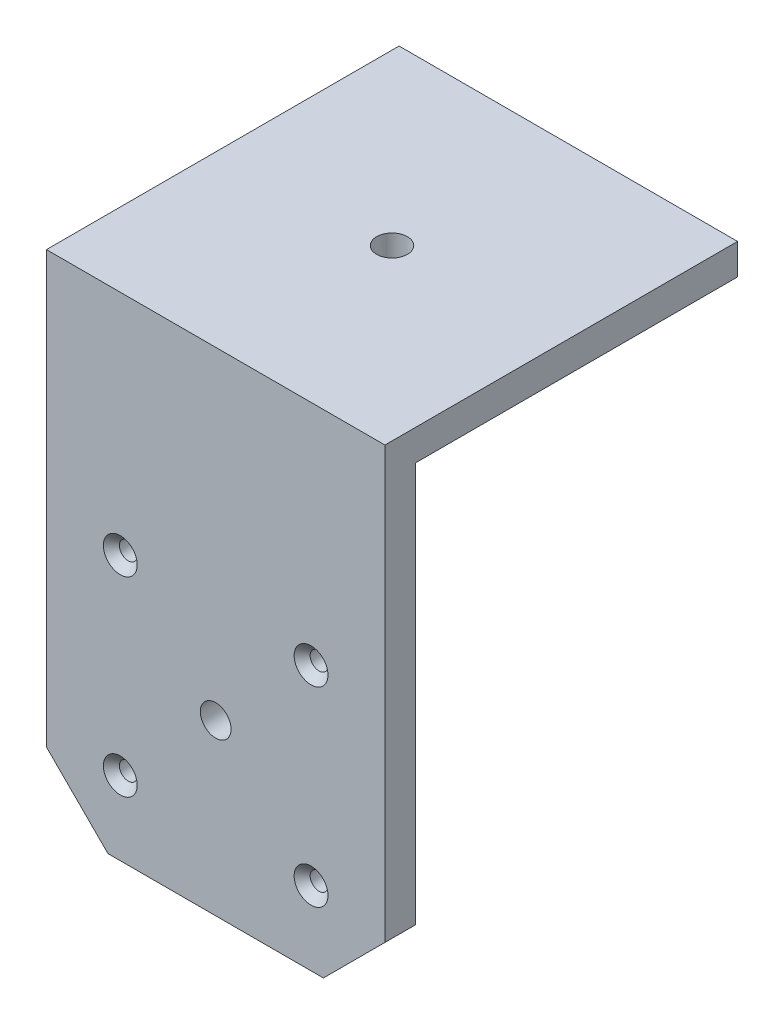
SolidWorks part; units mm, degrees
ref_plane "Ön Düzlem" through (0, 0, 0) normal (0, 0, 1) x (1, 0, 0)
ref_plane "Üst Düzlem" through (0, 0, 0) normal (0, 1, 0) x (1, 0, 0)
ref_plane "Sağ Düzlem" through (0, 0, 0) normal (1, 0, 0) x (0, 0, -1)
sketch "Sketch1" plane through (0, 0, 0) normal (0, 1, 0) x (1, 0, 0)
  line L1 (-27.5, 28.65) -> (27.5, 28.65)
  line L2 (-27.5, 28.65) -> (-27.5, -28.65)
  line L3 (-27.5, -28.65) -> (27.5, -28.65)
  line L4 (27.5, 28.65) -> (27.5, -28.65)
  line L5 (-27.5, 28.65) -> (27.5, -28.65) construction
  line L6 (-27.5, -28.65) -> (27.5, 28.65) construction
  circle A0 centre (0, 0) radius 2.5
  point P0 (0, 0)
  dimension "D1" = 55
  dimension "D2" = 57.3
extrude "Boss-Extrude1" add sketch "Sketch1" along normal blind 5
sketch "Sketch2" plane through (0, 0, 0) normal (0, -1, 0) x (1, 0, 0)
  line L0 (27.5, 28.65) -> (27.5, -28.65) construction
  line L1 (-27.5, 28.65) -> (27.5, 28.65)
  line L2 (-27.5, 28.65) -> (-27.5, 23.65)
  line L3 (-27.5, 23.65) -> (27.5, 23.65)
  line L4 (27.5, 28.65) -> (27.5, 23.65)
  line L6 (-27.5, -28.65) -> (27.5, -28.65)
  line L7 (-27.5, -28.65) -> (-27.5, -23.65)
  line L8 (-27.5, -23.65) -> (27.5, -23.65)
  line L9 (27.5, -28.65) -> (27.5, -23.65)
  dimension "D1" = 5
  dimension "D2" = 5
extrude "Boss-Extrude2" add sketch "Sketch2" along normal blind 75
sketch "Sketch3" plane through (0, 0, 28.65) normal (0, 0, 1) x (1, 0, 0)
  line L0 (-27.5, -75) -> (-17.5, -75)
  line L1 (27.5, -75) -> (-27.5, -75) construction
  line L2 (-17.5, -75) -> (-27.5, -65)
  line L3 (-27.5, 5) -> (-27.5, -75) construction
  line L4 (-27.5, -65) -> (-27.5, -75)
  line L5 (27.5, -75) -> (27.5, -65)
  line L6 (27.5, 5) -> (27.5, -75) construction
  line L7 (27.5, -65) -> (17.5, -75)
  line L8 (17.5, -75) -> (27.5, -75)
  dimension "D1" = 10
  dimension "D2" = 10
  dimension "D3" = 10
  dimension "D4" = 10
extrude "Cut-Extrude1" cut sketch "Sketch3" against normal up to next
sketch "Sketch4" plane through (0, 0, -23.65) normal (0, 0, 1) x (1, 0, 0)
  line L0 (-27.5, -75) -> (-17.5, -75)
  line L1 (-17.5, -75) -> (-27.5, -65)
  line L2 (-27.5, -65) -> (-27.5, -75)
  line L3 (17.5, -75) -> (27.5, -75)
  line L4 (27.5, -75) -> (27.5, -65)
  line L5 (27.5, -65) -> (17.5, -75)
  line L6 (17.5, -75) -> (17.494, -75.0141)
  line M2 (-27.5, 0) -> (-27.5, -75)
  line M3 (-27.5, -75) -> (27.5, -75)
  line M4 (27.5, -75) -> (27.5, 0)
extrude "Cut-Extrude2" cut sketch "Sketch4" against normal up to next contours L1 M3 M2 | L5 M4 M3
sketch "Sketch5" plane through (0, 0, 28.65) normal (0, 0, 1) x (1, 0, 0)
  line L0 (17.5, -75) -> (-17.5, -75) construction
  circle A0 centre (0, -47.5) radius 2.5
  dimension "D1" = 5
  dimension "D2" = 27.5
extrude "Cut-Extrude3" cut sketch "Sketch5" against normal up to next
sketch "Sketch6" plane through (0, 0, -28.65) normal (0, 0, -1) x (-1, 0, 0)
  circle A0 centre (0, -47.5) radius 2.5
extrude "Cut-Extrude4" cut sketch "Sketch6" against normal up to next
sketch "Sketch7" plane through (0, 0, -23.65) normal (0, 0, 1) x (1, 0, 0)
  line L0 (-27.5, 0) -> (27.5, 0)
  line L1 (27.5, 0) -> (27.5, -65)
  line L2 (27.5, -65) -> (17.5, -75)
  line L3 (17.5, -75) -> (-17.5, -75)
  line L4 (-17.5, -75) -> (-27.5, -65)
  line L5 (-27.5, -65) -> (-27.5, 0)
extrude "Cut-Extrude5" cut sketch "Sketch7" against normal up to next
hole_wizard "CSK for M2.5 Flat Head Machine Screw1" positions "Sketch9" profile "Sketch8" countersink size "M2.5" standard "ANSI Metric" end condition up to next
sketch "Sketch9" plane through (0, 0, 28.65) normal (0, 0, 1) x (1, 0, 0)
  point P0 (-15.5, -32)
  point P3 (15.5, -32)
  point P6 (-15.5, -63)
  point P9 (15.5, -63)
sketch "Sketch8" plane through (-15.5, -32, 28.65) normal (1, 0, 0) x (0, -1, 0)
  line L0 (0, 0) -> (0, 5)
  line L1 (0, 5) -> (1.45, 5)
  line L2 (1.45, 5) -> (1.45, 1.3)
  line L3 (1.45, 1.3) -> (2.75, 0)
  line L5 (2.75, 0) -> (0, 0)
  line L6 (-1.45, 1.3) -> (-2.75, 0) construction
  line L11 (0, -6.35) -> (0, 107.95) construction
  dimension "Thru Hole Dia." = 2.9
  dimension "Thru Hole Depth" = 5
  dimension "Near C'Sink Dia." = 5.5
  dimension "Near C'Sink Angle" = 90
hole_wizard "#6-40 Tapped Hole1" positions "Sketch11" profile "Sketch10" tap size "#6-40" standard "ANSI Inch"
sketch "Sketch11" plane through (0, 0, 0) normal (0, -1, 0) x (-1, 0, 0)
  point P0 (-15.5, 16.15)
  point P3 (15.5, 16.15)
sketch "Sketch10" plane through (15.5, 0, -16.15) normal (1, 0, 0) x (0, 0, -1)
  line L0 (0, 0) -> (0, 4.3623)
  line L1 (0, 4.3623) -> (1.4351, 3.5)
  line L2 (1.4351, 3.5) -> (1.4351, 0)
  line L5 (1.4351, 0) -> (0, 0)
  line L10 (0, 4.3623) -> (-1.4351, 3.5) construction
  line L11 (0, -6.35) -> (0, 107.95) construction
  dimension "Tap Drill Dia." = 2.8702
  dimension "Tap Drill Depth" = 3.5
  dimension "Drill Angle" = 118
